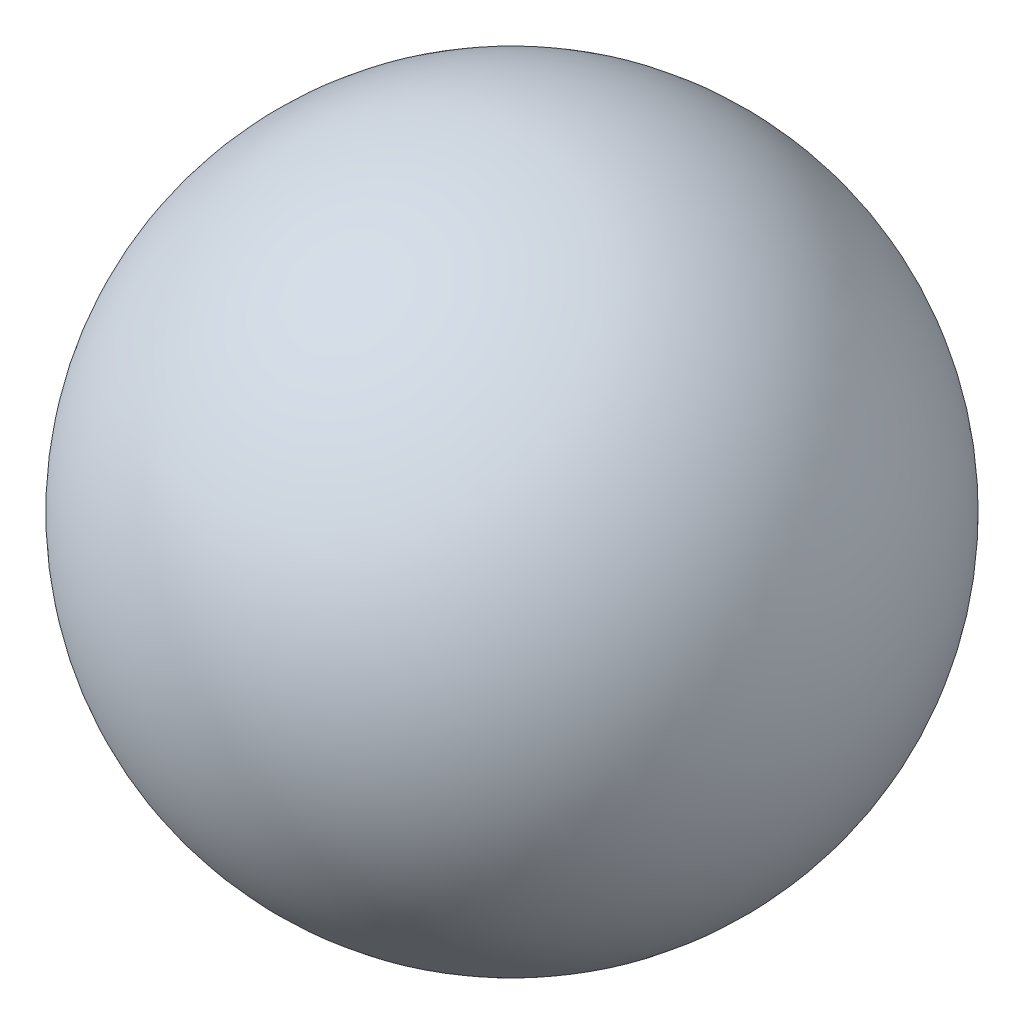
SolidWorks part; units mm, degrees
ref_plane "Front Plane" through (0, 0, 0) normal (0, 0, 1) x (1, 0, 0)
ref_plane "Top Plane" through (0, 0, 0) normal (0, 1, 0) x (1, 0, 0)
ref_plane "Right Plane" through (0, 0, 0) normal (1, 0, 0) x (0, 0, -1)
sketch "Sketch2" plane through (-2.698, 34.4758, 6.7617) normal (1, 0, 0) x (0, 0, 1)
  line L0 (-9.0565, -4.0236) -> (30.5435, -4.0236) construction
  line L1 (-4.7065, -4.0236) -> (-13.4065, -4.0236) construction
  line L2 (30.5435, -17.3236) -> (30.5435, 39.6764)
  line L4 (-2.9565, 33.6764) -> (-15.1222, 33.6764) construction
  circle A0 centre (30.5435, 11.1764) radius 28.5
  point P8 (30.5435, 39.6764)
  dimension "D1" = 57
  dimension "D2" = 39.6
  dimension "D3" = 6
revolve "Revolve3" add sketch "Sketch2" angle 360 about L2
